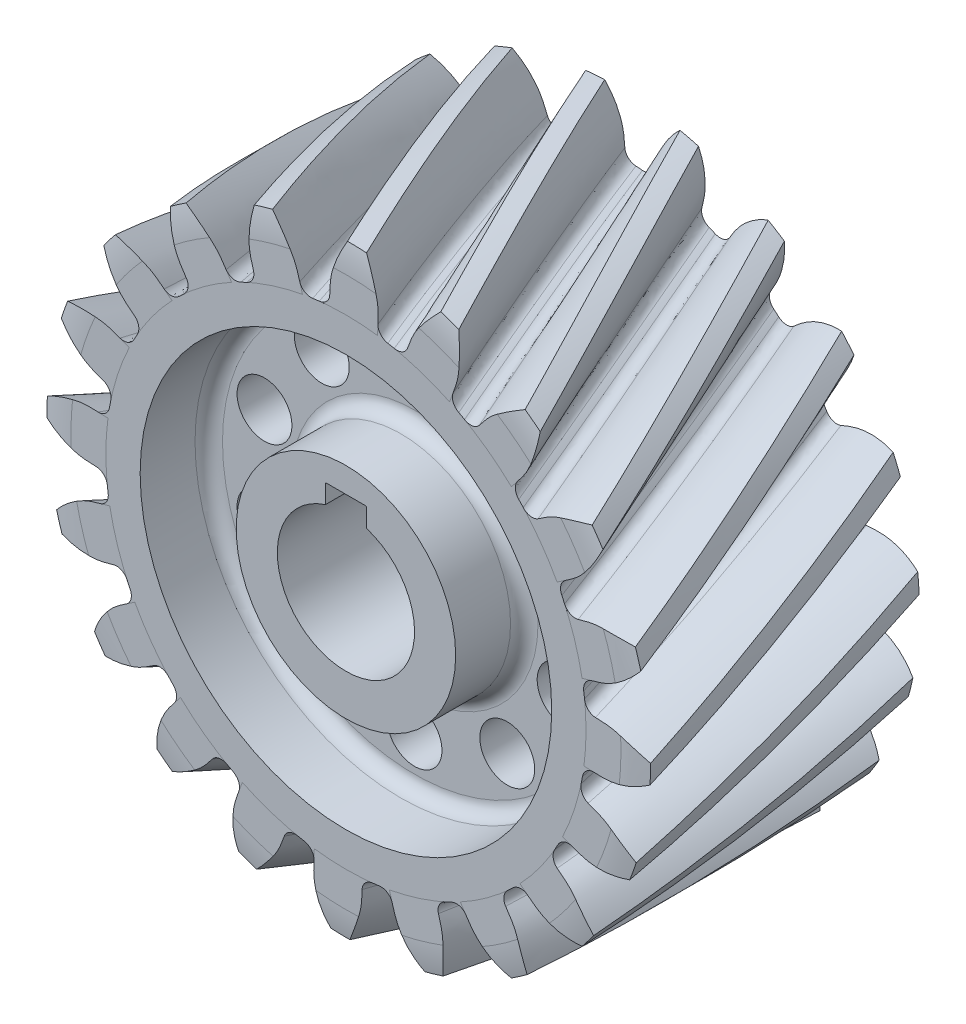
SolidWorks part; units mm, degrees
material "Plain Carbon Steel"
ref_plane "Front Plane" through (0, 0, 0) normal (0, 0, 1) x (1, 0, 0)
ref_plane "Top Plane" through (0, 0, 0) normal (0, 1, 0) x (1, 0, 0)
ref_plane "Right Plane" through (0, 0, 0) normal (1, 0, 0) x (0, 0, -1)
ref_axis "Axis1" through (0, 0, -0.5) along (0, 0, 1)
ref_plane "Plane1" through (0, 0, 20) normal (0, 0, 1) x (1, 0, 0)
ref_plane "Plane2" through (0, 0, 10) normal (0, 0, 1) x (1, 0, 0)
sketch "Sketch1" plane through (0, 0, 0) normal (0, 0, 1) x (1, 0, 0)
  line L0 (-6.4279, 17.6604) -> (6.4279, 22.3396) construction
  line L1 (24.2, 0) -> (-24.2, 0) construction
  line L2 (0, 0) -> (-6.4279, 17.6604) construction
  line L3 (0, 0) -> (-7.6441, 17.169) construction
  line L4 (0, 0) -> (-8.8232, 16.594) construction
  line L5 (0, 0) -> (-9.9592, 15.9381) construction
  line L6 (0, 0) -> (-11.0467, 15.2045) construction
  line L7 (-7.6441, 17.169) -> (-0.1965, 20.4849) construction
  line L8 (-8.8232, 16.594) -> (-0.4665, 21.0373) construction
  line L9 (-9.9592, 15.9381) -> (-0.8202, 21.6488) construction
  line L10 (-11.0467, 15.2045) -> (-1.2668, 22.3101) construction
  line L11 (0, 0) -> (-12.0805, 14.3969) construction
  line L12 (-12.0805, 14.3969) -> (-1.8149, 23.0107) construction
  line L13 (-5.1803, 18.0658) -> (0, 0) construction
  line L14 (-5.1803, 18.0658) -> (0.1339, 19.5896) construction
  circle A0 centre (0, 0) radius 20 construction
  circle A1 centre (0, 0) radius 18.7939 construction
  circle A2 centre (0, 0) radius 22 construction
  arc A3 (0.2801, 18.7918) -> (-6.4279, 17.6604) centre (0, 0) ccw construction
  circle A4 centre (0, 0) radius 17.5 construction
  point P3 (0, 20)
  dimension "D1" = 40
  dimension "D9" = 37.5877
  dimension "D10" = 9.4645
  dimension "D18" = 44
  dimension "D19" = 35
  dimension "D2" = 20
  dimension "D3" = 8.1525
  dimension "D4" = 4
  dimension "D5" = 4
  dimension "D6" = 4
  dimension "D7" = 4
  dimension "D8" = 6.8404
  dimension "D11" = 10.7766
  dimension "D12" = 12.0886
  dimension "D13" = 4
  dimension "D14" = 13.4007
  dimension "D15" = 4
  dimension "D16" = 5.5283
  dimension "D17" = 6.8404
sketch "Sketch2" plane through (0, 0, 0) normal (0, 0, 1) x (1, 0, 0)
  line L0 (0, 0) -> (-2.6629, 33.8348) construction
  line L1 (0, -24.7559) -> (0, 24.7559) construction
  line L2 (-3.2163, 18.5166) -> (-3.1143, 17.2207)
  line L3 (0.2801, 18.7918) -> (0.3821, 17.4958)
  circle A0 centre (0, 0) radius 17.5 construction
  spline S0 degree 3 poles (0.2801, 18.7918) (0.2503, 19.2086) (0.0965, 19.7799) (-0.2029, 20.5155) (-0.5915, 21.3068) (-0.9723, 21.9043) (-1.2668, 22.3101) knots 0 0 0 0 0.319878 0.454552 0.612797 1 1 1 1
  spline S1 degree 3 poles (-3.2163, 18.5166) (-3.2521, 18.933) (-3.1895, 19.5213) (-3.0089, 20.2947) (-2.7489, 21.137) (-2.4663, 21.7867) (-2.2388, 22.2336) knots 0 0 0 0 0.319878 0.454552 0.612797 1 1 1 1
  dimension "D1" = 4.5
sketch "Sketch3" plane through (0, 0, 0) normal (0, 0, 1) x (1, 0, 0)
  arc A0 (-1.0327, 21.9757) -> (-2.4178, 21.8667) centre (0, 0) ccw
  circle A1 centre (0, 0) radius 22 construction
  circle A2 centre (0, 0) radius 17.5 construction
  arc A7 (0.3821, 17.4958) -> (-3.1143, 17.2207) centre (0, 0) ccw
  spline S0 degree 3 poles (0.2801, 18.7918) (0.2503, 19.2086) (0.0965, 19.7799) (-0.2029, 20.5155) (-0.5915, 21.3068) (-0.9723, 21.9043) (-1.2668, 22.3101) knots 0 0 0 0 0.319878 0.454552 0.612797 1 1 1 1 construction
  spline S1 degree 3 poles (-3.2163, 18.5166) (-3.2521, 18.933) (-3.1895, 19.5213) (-3.0089, 20.2947) (-2.7489, 21.137) (-2.4663, 21.7867) (-2.2388, 22.2336) knots 0 0 0 0 0.319878 0.454552 0.612797 1 1 1 1 construction
  spline S2 degree 3 poles (0.3821, 17.4958) (0.3191, 18.186) (0.3209, 19.0602) (-0.0062, 20.0304) (-0.2027, 20.5156) (-0.5316, 21.1846) (-0.8282, 21.6729) (-1.0327, 21.9757) knots 0 0 0 0 0.441913 0.532273 0.641803 0.770504 1 1 1 1
  spline S3 degree 3 poles (-3.1143, 17.2207) (-3.1601, 17.9121) (-3.2987, 18.7753) (-3.1274, 19.7848) (-3.0092, 20.2947) (-2.7889, 21.0069) (-2.5724, 21.5356) (-2.4178, 21.8667) knots 0 0 0 0 0.441913 0.532273 0.641803 0.770504 1 1 1 1
  point P5 (-1.0327, 21.9757)
  point P8 (-2.4178, 21.8667)
sketch "Sketch4" plane through (0, 0, 0) normal (0, 0, 1) x (1, 0, 0)
  circle A0 centre (0, 0) radius 17.5
  circle A1 centre (0, 0) radius 17.5 construction
extrude "Boss-Extrude2" add sketch "Sketch4" along normal up to surface (20 mm away) up to plane "Plane1"
sketch "Sketch9" plane through (0, 0, 20) normal (0, 0, 1) x (1, 0, 0)
  line L0 (-13.1308, 13.4459) -> (-3.3429, 23.0043) construction
  line L1 (-8.2368, 18.2251) -> (0, 0) construction
  line L2 (0, 0) -> (-13.1308, 13.4459) construction
  line L3 (0, 0) -> (-14.0367, 12.4972) construction
  line L4 (0, 0) -> (-14.8743, 11.4876) construction
  line L5 (0, 0) -> (-15.6394, 10.422) construction
  line L6 (0, 0) -> (-16.3283, 9.3057) construction
  line L7 (-14.0367, 12.4972) -> (-8.6156, 18.5861) construction
  line L8 (-14.8743, 11.4876) -> (-9.0892, 18.9782) construction
  line L9 (-15.6394, 10.422) -> (-9.6633, 19.3898) construction
  line L10 (-16.3283, 9.3057) -> (-10.3426, 19.8084) construction
  line L11 (0, 0) -> (-16.9376, 8.144) construction
  line L12 (-16.9376, 8.144) -> (-11.1307, 20.2212) construction
  line L13 (-12.1608, 14.3291) -> (0, 0) construction
  line L14 (-12.1608, 14.3291) -> (-7.9458, 17.9063) construction
  line L15 (-12.0805, 14.3969) -> (-1.8149, 23.0107) construction
  line L16 (-11.0467, 15.2045) -> (-1.2668, 22.3101) construction
  line L17 (-9.9592, 15.9381) -> (-0.8202, 21.6488) construction
  line L18 (-8.8232, 16.594) -> (-0.4665, 21.0373) construction
  line L19 (-7.6441, 17.169) -> (-0.1965, 20.4849) construction
  line L20 (-5.1803, 18.0658) -> (0.1339, 19.5896) construction
  line L21 (0, 0) -> (-10.6055, 19.2749) construction
  line L23 (-7.484, 17.2394) -> (-6.8573, 16.1005) construction
  line L24 (0, 0) -> (-2.6629, 33.8348) construction
  circle A0 centre (0, 0) radius 20 construction
  circle A1 centre (0, 0) radius 18.7939 construction
  circle A2 centre (0, 0) radius 22 construction
  arc A3 (-7.484, 17.2394) -> (-13.1308, 13.4459) centre (0, 0) ccw construction
  circle A4 centre (0, 0) radius 17.5 construction
  circle A5 centre (0, 0) radius 18.7939 construction
  point P3 (-8.2368, 18.2251)
  dimension "D1" = 40
  dimension "D9" = 37.5877
  dimension "D10" = 6.8404
  dimension "D18" = 44
  dimension "D19" = 35
  dimension "D2" = 4.5
  dimension "D3" = 24.321
  dimension "D4" = 4
  dimension "D5" = 4
  dimension "D6" = 4
  dimension "D7" = 4
  dimension "D8" = 6.8404
  dimension "D11" = 6.8404
  dimension "D13" = 4
  dimension "D15" = 4
sketch "Sketch10" plane through (0, 0, 20) normal (0, 0, 1) x (1, 0, 0)
  line L0 (-10.6055, 19.2749) -> (0, 0) construction
  line L1 (-13.1308, 13.4459) -> (-3.3429, 23.0043) construction
  circle A0 centre (0, 0) radius 22 construction
  spline S0 degree 3 poles (-6.8573, 16.1005) (-7.199, 16.7035) (-7.5573, 17.5008) (-8.255, 18.2503) (-8.6339, 18.6114) (-9.3142, 19.1722) (-9.907, 19.56) (-10.3426, 19.8084) knots 0 0 0 0 0.407137 0.490386 0.591297 0.709869 1 1 1 1
  spline S1 degree 3 poles (-9.9302, 14.4098) (-10.2566, 15.0211) (-10.7384, 15.7506) (-10.998, 16.741) (-11.1003, 17.2543) (-11.2099, 18.1292) (-11.2202, 18.8375) (-11.1969, 19.3384) knots 0 0 0 0 0.407137 0.490386 0.591297 0.709869 1 1 1 1
  point P29 (-11.2089, 18.9304)
  point P30 (-9.9915, 19.6002)
sketch "Sketch12" plane through (0, 0, 20) normal (0, 0, 1) x (1, 0, 0)
  arc A0 (-6.8573, 16.1005) -> (-9.9302, 14.4098) centre (0, 0) ccw
  arc A1 (-9.9915, 19.6002) -> (-11.2089, 18.9304) centre (0, 0) ccw
  spline S0 degree 3 poles (-6.8573, 16.1005) (-7.199, 16.7035) (-7.5573, 17.5008) (-8.255, 18.2503) (-8.6339, 18.6114) (-9.2092, 19.0856) (-9.6805, 19.4084) (-9.9915, 19.6002) knots 0 0 0 0 0.441915 0.532275 0.641806 0.770507 1 1 1 1
  spline S1 degree 3 poles (-11.2089, 18.9304) (-11.2133, 18.565) (-11.193, 17.9941) (-11.1003, 17.2543) (-10.998, 16.741) (-10.7384, 15.7506) (-10.2566, 15.0211) (-9.9302, 14.4098) knots 0 0 0 0 0.229493 0.358194 0.467725 0.558085 1 1 1 1
sketch "Sketch13" plane through (0, 0, 0) normal (0, 0, 1) x (1, 0, 0)
  circle A0 centre (0, 0) radius 20
curve "Helix/Spiral1" pitch 296.0451 height 20 turns 0.0676
sweep "Sweep1" add profiles "Sketch3" path "Helix/Spiral1"
fillet "Fillet1" radius 0.8 2 edges
pattern_circular "CirPattern1" count 20 over 360 about axis through (0, 0, -0.5) along (0, 0, 1) of "Sweep1", "Fillet1"
sketch "Sketch5" plane through (0, 0, 0) normal (0, 0, 1) x (1, 0, 0)
  line L1 (-1.4, 6.1697) -> (1.4, 6.1697)
  line L2 (-1.5, 6.0697) -> (-1.5, 4.7697)
  line L4 (1.5, 6.0697) -> (1.5, 4.7697)
  arc A0 (-1.5, 4.7697) -> (1.5, 4.7697) centre (0, 0) ccw
  arc A1 (-1.4, 6.1697) -> (-1.5, 6.0697) centre (-1.4, 6.0697) ccw
  arc A2 (1.4, 6.1697) -> (1.5, 6.0697) centre (1.4, 6.0697) cw
  point P9 (-1.5, 6.1697)
  point P12 (1.5, 6.1697)
  dimension "D1" = 10
  dimension "D4" = 0.1
  dimension "D2" = 3
  dimension "D3" = 1.4
extrude "Cut-Extrude2" cut sketch "Sketch5" along normal through all
sketch "Sketch6" plane through (0, 0, 0) normal (1, 0, 0) x (0, 0, -1)
  line L0 (0, 24.2012) -> (0, -24.2012) construction
  line L1 (0, 15) -> (-4, 15)
  line L2 (0, 15) -> (0, 8)
  line L3 (0, 8) -> (-4, 8)
  line L4 (-5, 14) -> (-5, 9)
  line L5 (-18.1693, 0) -> (8.9191, 0) construction
  line L6 (5.9717, 0) -> (-5.9717, 0) construction
  arc A0 (-4, 8) -> (-5, 9) centre (-4, 9) cw
  arc A1 (-4, 15) -> (-5, 14) centre (-4, 14) ccw
  point P16 (-5, 15)
  dimension "D4" = 1
  dimension "D1" = 30
  dimension "D2" = 16
  dimension "D3" = 5
revolve "Cut-Revolve1" cut sketch "Sketch6" angle 360 about L5
sketch "Sketch7" plane through (0, 0, 0) normal (0, 1, 0) x (1, 0, 0)
  line L0 (-18, 0) -> (-20, 0)
  line L1 (-46.1897, 0) -> (46.1897, 0) construction
  line L2 (-24, -0.8348) -> (-24, 2)
  line L3 (-24, 2) -> (-18, 2)
  line L4 (-18, 2) -> (-18, 0)
  line L5 (0, 6.1489) -> (0, -13.1749) construction
  line L6 (0, -5.5) -> (0, 5.5) construction
  arc A0 (-20, 0) -> (-24, -0.8348) centre (-20, -10) ccw
  dimension "D5" = 10
  dimension "D1" = 2
  dimension "D2" = 36
  dimension "D3" = 2
  dimension "D4" = 6
revolve "Cut-Revolve2" cut sketch "Sketch7" angle 360 about L5
mirror "Mirror1" about plane through (0, 0, 10) normal (0, 0, 1) of "Cut-Revolve2", "Cut-Revolve1"
sketch "Sketch14" plane through (0, 0, 15) normal (0, 0, 1) x (1, 0, 0)
  line L0 (11.4608, 0) -> (-11.4608, 0) construction
  line L1 (0, -11.4608) -> (0, 11.4608) construction
  circle A0 centre (0, 11.5) radius 2
  dimension "D2" = 4
  dimension "D1" = 11.5
extrude "Cut-Extrude3" cut sketch "Sketch14" against normal blind 10
pattern_circular "CirPattern2" count 10 over 360 about axis through (0, 0, 0) along (0, 0, 1) of "Cut-Extrude3"
equation "\"D1@Sketch1\"=\"module\"*\"teeth\""
equation "\"D2@Sketch1\"=\"pressure\""
equation "\"D3@Sketch1\"=(4*((\"D9@Sketch1\"*pi)/360))+\"D8@Sketch1\""
equation "\"D10@Sketch1\"=(8*((\"D9@Sketch1\"*pi)/360))+\"D8@Sketch1\""
equation "\"D11@Sketch1\"=(12*((\"D9@Sketch1\"*pi)/360))+\"D8@Sketch1\""
equation "\"D12@Sketch1\"=(16*((\"D9@Sketch1\"*pi)/360))+\"D8@Sketch1\""
equation "\"D14@Sketch1\"=(20*((\"D9@Sketch1\"*pi)/360))+\"D8@Sketch1\""
equation "\"D16@Sketch1\"=\"D8@Sketch1\"-(4*((\"D9@Sketch1\"*pi)/360))"
equation "\"D17@Sketch1\"=\"D8@Sketch1\""
equation "\"D1@Sketch2\"=(360/\"teeth\")/4"
equation "\"D18@Sketch1\"=\"D1@Sketch1\"+(\"MODULE\"*2)"
equation "\"D19@Sketch1\"=\"D1@Sketch1\"-(\"MODULE\"*2.5)"
equation "\"D1@Plane1\" = \"thickness\""
equation "\"D1@Sketch6\"=(\"module\"*\"teeth\")-(\"module\"*5)"
equation "\"D3@Sketch6\"=\"thickness\"/4"
equation "\"D1@Plane2\"=\"thickness\"/2"
equation "\"D2@Sketch7\"=(\"module\"*\"teeth\")-(\"module\"*2)"
equation "\"D3@Sketch7\"=\"module\""
equation "\"D4@Sketch7\"=\"module\"*3"
equation "\"D5@Sketch7\"=\"module\"*5"
equation "\"D2@Sketch9\" = ( 360 / \"teeth\" ) / 4"
equation "\"D11@Sketch9\"=\"D10@Sketch9\""
equation "\"D3@Sketch9\"=(( \"thickness\" * tan ( \"helix\" )) / ( ( pi * \"module\" * \"teeth\" ) / 360 ))"
equation "\"D5@Helix/Spiral1\"=(\"thickness\"*tan(\"helix\"))/(\"module\"*\"teeth\"*pi)"
equation "\"D3@Helix/Spiral1\"=\"thickness\""
